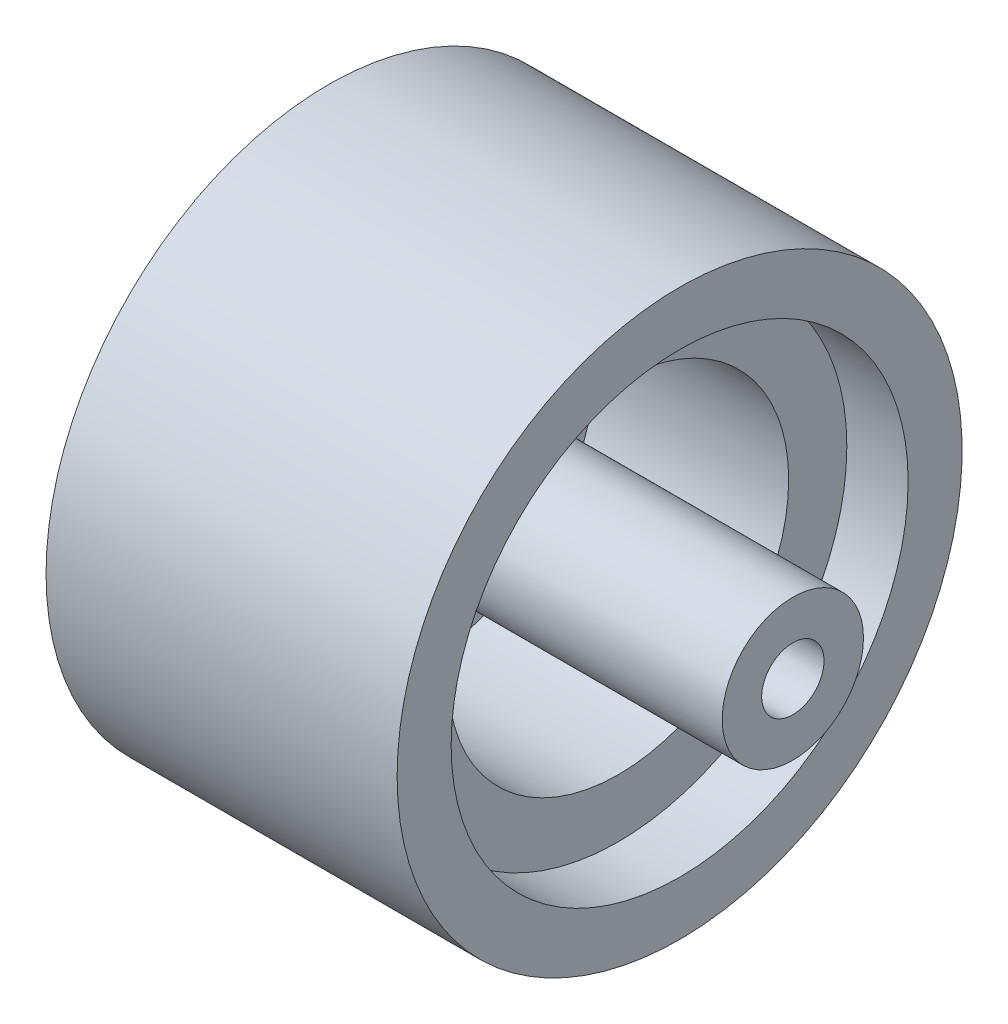
SolidWorks part; units mm, degrees
ref_plane "正面" through (0, 0, 0) normal (0, 0, 1) x (1, 0, 0)
ref_plane "平面" through (0, 0, 0) normal (0, 1, 0) x (1, 0, 0)
ref_plane "右側面" through (0, 0, 0) normal (1, 0, 0) x (0, 0, -1)
sketch "ｽｹｯﾁ1" plane through (0, 0, 0) normal (1, 0, 0) x (0, 0, -1)
  circle A0 centre (0, 0) radius 11
  dimension "D1" = 22
extrude "ﾎﾞｽ - 押し出し1" add sketch "ｽｹｯﾁ1" along normal blind 11 contours A0
sketch "ｽｹｯﾁ2" plane through (11, 0, 0) normal (1, 0, 0) x (0, 0, -1)
  circle A0 centre (0, 0) radius 8.2
  circle A1 centre (0, 0) radius 11 construction
  dimension "D1" = 2.8
extrude "ｶｯﾄ - 押し出し1" cut sketch "ｽｹｯﾁ2" against normal blind 9.35
sketch "ｽｹｯﾁ3" plane through (0, 0, 0) normal (-1, 0, 0) x (0, 0, 1)
  circle A0 centre (4.6857, 6.4842) radius 2
  dimension "D2" = 4
  dimension "D1" = 8
sketch "ｽｹｯﾁ4" plane through (1.65, 0, 0) normal (1, 0, 0) x (0, 0, -1)
  circle A0 centre (0, 0) radius 3.4
  dimension "D1" = 6.8
extrude "ﾎﾞｽ - 押し出し2" add sketch "ｽｹｯﾁ4" along normal blind 17.75
sketch "ｽｹｯﾁ5" plane through (19.4, 0, 0) normal (1, 0, 0) x (0, 0, -1)
  circle A0 centre (0, 0) radius 1.5
  dimension "D1" = 3
extrude "ｶｯﾄ - 押し出し4" cut sketch "ｽｹｯﾁ5" against normal blind 25.75
sketch "ｽｹｯﾁ6" plane through (0, 0, 0) normal (-1, 0, 0) x (0, 0, 1)
  circle A0 centre (0, 0) radius 13.6
  circle A1 centre (0, 0) radius 11
  dimension "D1" = 27.2
  dimension "D2" = 22
extrude "ﾎﾞｽ - 押し出し4" add sketch "ｽｹｯﾁ6" against normal blind 13.95 and the other way blind 2.95
